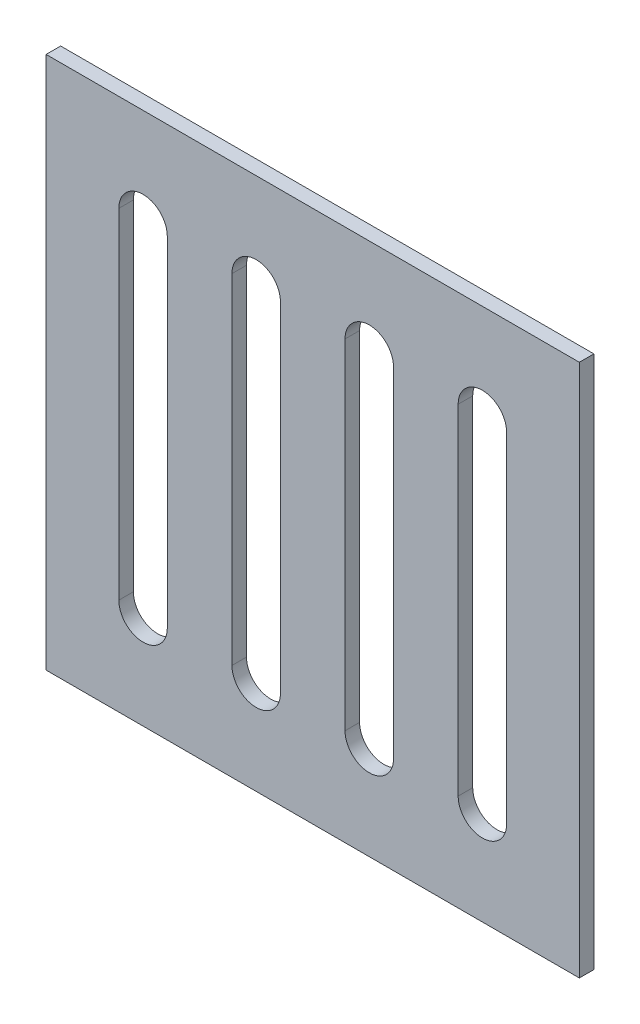
SolidWorks part; units mm, degrees
ref_plane "Ön Düzlem" through (0, 0, 0) normal (0, 0, 1) x (1, 0, 0)
ref_plane "Üst Düzlem" through (0, 0, 0) normal (0, 1, 0) x (1, 0, 0)
ref_plane "Sağ Düzlem" through (0, 0, 0) normal (1, 0, 0) x (0, 0, -1)
sketch "Çizim1" plane through (0, 0, 0) normal (0, 0, 1) x (1, 0, 0)
  line L1 (0, 0) -> (110, 0)
  line L2 (0, 0) -> (0, -110)
  line L3 (0, -110) -> (110, -110)
  line L4 (110, 0) -> (110, -110)
  dimension "D1" = 110
  dimension "D2" = 110
extrude "Yükseklik-Ekstrüzyon1" add sketch "Çizim1" along normal blind 3
sketch "Çizim2" plane through (0, 0, 3) normal (0, 0, 1) x (1, 0, 0)
  line L0 (20, -20) -> (20, -90) construction
  line L1 (25, -20) -> (25, -90)
  line L2 (15, -20) -> (15, -90)
  line L3 (0, 0) -> (0, -110) construction
  line L5 (38.3333, -20) -> (38.3333, -90)
  line L6 (48.3333, -20) -> (48.3333, -90)
  line L7 (43.3333, -20) -> (43.3333, -90) construction
  line L8 (61.6667, -20) -> (61.6667, -90)
  line L9 (71.6667, -20) -> (71.6667, -90)
  line L10 (66.6667, -20) -> (66.6667, -90) construction
  line L11 (85, -20) -> (85, -90)
  line L12 (95, -20) -> (95, -90)
  line L13 (90, -20) -> (90, -90) construction
  line L14 (110, -110) -> (110, 0) construction
  arc A0 (25, -20) -> (15, -20) centre (20, -20) ccw
  arc A1 (15, -90) -> (25, -90) centre (20, -90) ccw
  arc A2 (48.3333, -20) -> (38.3333, -20) centre (43.3333, -20) ccw
  arc A3 (38.3333, -90) -> (48.3333, -90) centre (43.3333, -90) ccw
  arc A4 (71.6667, -20) -> (61.6667, -20) centre (66.6667, -20) ccw
  arc A5 (61.6667, -90) -> (71.6667, -90) centre (66.6667, -90) ccw
  arc A6 (95, -20) -> (85, -20) centre (90, -20) ccw
  arc A7 (85, -90) -> (95, -90) centre (90, -90) ccw
  point P2 (20, -55)
  point P9 (0, -55)
  point P13 (43.3333, -55)
  point P20 (66.6667, -55)
  point P27 (90, -55)
  dimension "D1" = 10
  dimension "D2" = 70
  dimension "D3" = 15
  dimension "D5" = 15
  dimension "D4" = 4
extrude "Kes-Ekstrüzyon1" cut sketch "Çizim2" against normal blind 10
